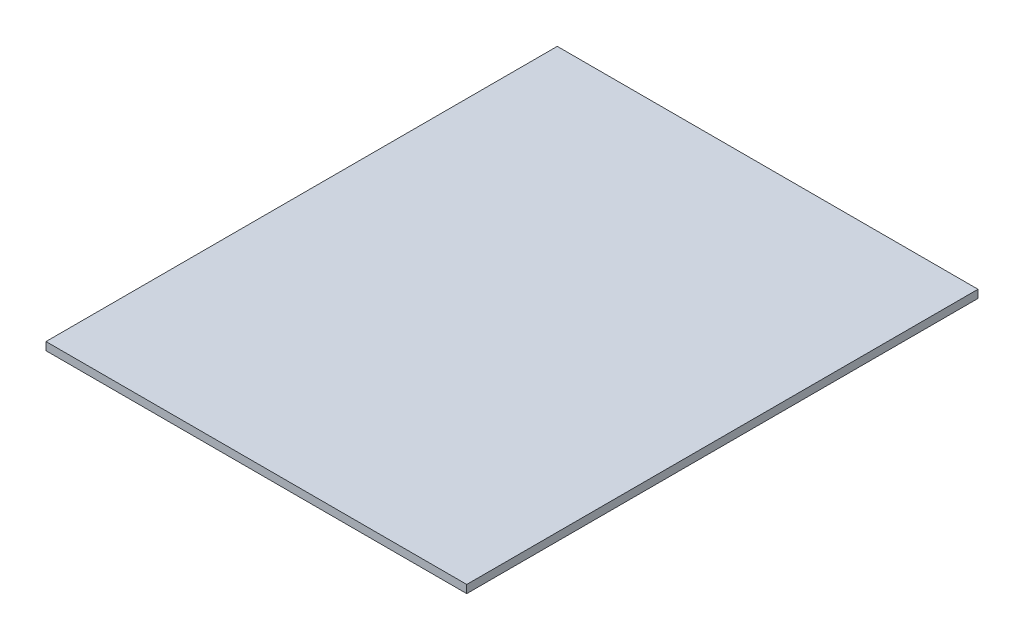
SolidWorks part; units mm, degrees
ref_plane "Front Plane" through (0, 0, 0) normal (0, 0, 1) x (1, 0, 0)
ref_plane "Top Plane" through (0, 0, 0) normal (0, 1, 0) x (1, 0, 0)
ref_plane "Right Plane" through (0, 0, 0) normal (1, 0, 0) x (0, 0, -1)
sketch "Sketch1" plane through (0, 0, 0) normal (0, 1, 0) x (1, 0, 0)
  line L1 (0, 0) -> (250.825, 0)
  line L2 (0, 0) -> (0, -304.8)
  line L3 (0, -304.8) -> (250.825, -304.8)
  line L4 (250.825, 0) -> (250.825, -304.8)
  dimension "D1" = 304.8
  dimension "D2" = 250.825
extrude "Boss-Extrude1" add sketch "Sketch1" along normal blind 4.7625 contours L1 L4 L3 L2
